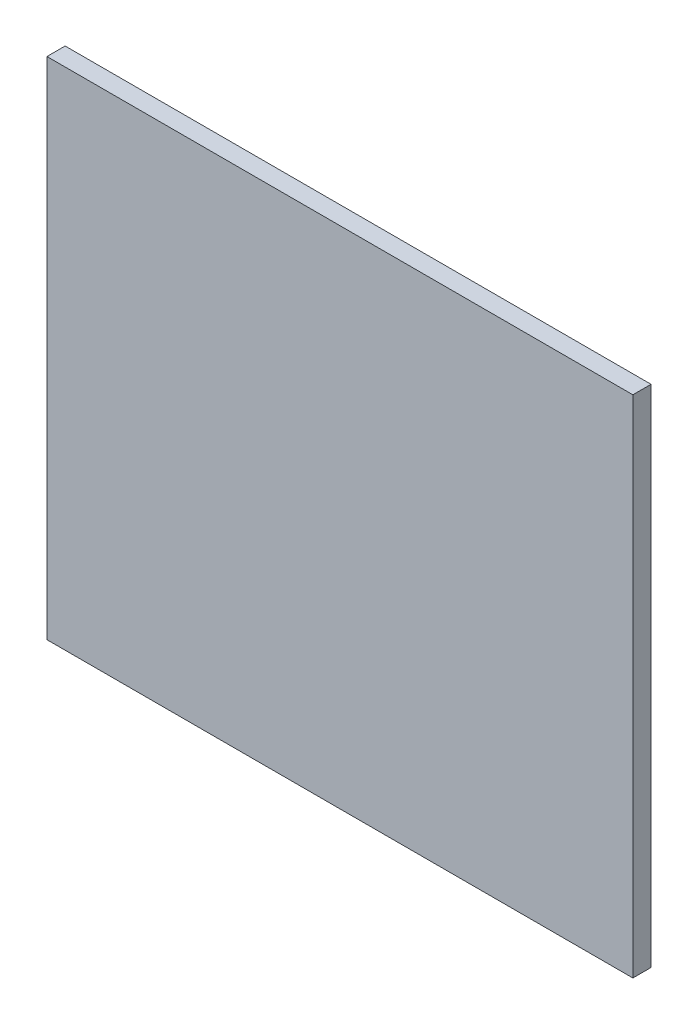
SolidWorks part; units mm, degrees
ref_plane "Front Plane" through (0, 0, 0) normal (0, 0, 1) x (1, 0, 0)
ref_plane "Top Plane" through (0, 0, 0) normal (0, 1, 0) x (1, 0, 0)
ref_plane "Right Plane" through (0, 0, 0) normal (1, 0, 0) x (0, 0, -1)
sketch "Sketch1" plane through (0, 0, 0) normal (0, 0, 1) x (1, 0, 0)
  line L1 (0, 0) -> (290, 0)
  line L2 (0, 0) -> (0, 250)
  line L3 (0, 250) -> (290, 250)
  line L4 (290, 0) -> (290, 250)
  dimension "D1" = 290
  dimension "D2" = 250
extrude "Boss-Extrude1" add sketch "Sketch1" along normal blind 9
